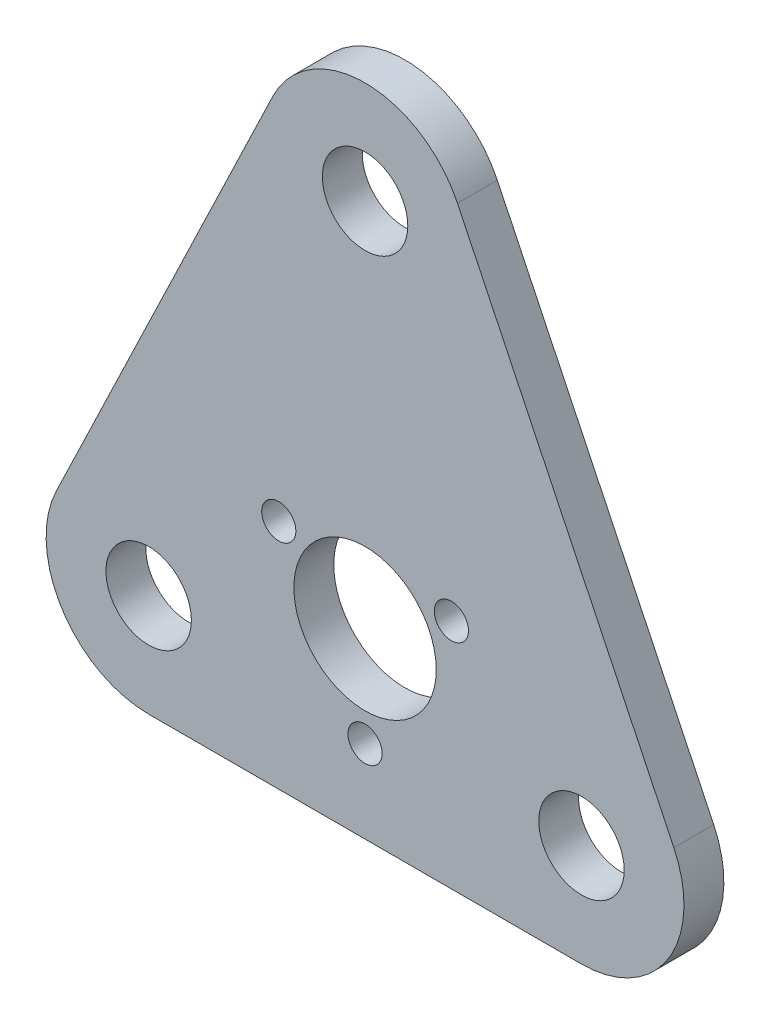
SolidWorks part; units mm, degrees
ref_plane "Front Plane" through (0, 0, 0) normal (0, 0, 1) x (1, 0, 0)
ref_plane "Top Plane" through (0, 0, 0) normal (0, 1, 0) x (1, 0, 0)
ref_plane "Right Plane" through (0, 0, 0) normal (1, 0, 0) x (0, 0, -1)
sketch "Sketch1" plane through (0, 0, 0) normal (0, 0, 1) x (1, 0, 0)
  line L0 (-38, 0) -> (38, 0) construction
  line L1 (-38, -18) -> (38, -18)
  line L2 (0, -18) -> (0, 14) construction
  line L3 (-32.3193, 14) -> (32.3193, 14) construction
  line L4 (0, 14) -> (-24.6565, 28.2354) construction
  line L5 (0, 14) -> (0, 79) construction
  line L6 (16.221, 86.8025) -> (54.221, 7.8025)
  line L7 (-16.221, 86.8025) -> (-54.221, 7.8025)
  circle A0 centre (-38, 0) radius 7.5
  circle A1 centre (38, 0) radius 7.5
  arc A2 (-54.221, 7.8025) -> (-38, -18) centre (-38, 0) ccw
  arc A3 (38, -18) -> (54.221, 7.8025) centre (38, 0) ccw
  circle A4 centre (0, 14) radius 12.5
  circle A6 centre (-15.1554, 22.75) radius 3
  circle A7 centre (0, -3.5) radius 3
  circle A8 centre (15.1554, 22.75) radius 3
  circle A9 centre (0, 79) radius 7.5
  arc A10 (16.221, 86.8025) -> (-16.221, 86.8025) centre (0, 79) ccw
  point P4 (0, 0)
  point P18 (0, 14)
  point P30 (-3.1358, 101.4343)
  dimension "D1" = 30
  dimension "D2" = 36
  dimension "D3" = 15
  dimension "D5" = 25
  dimension "D6" = 6
  dimension "D7" = 6
  dimension "D8" = 6
  dimension "D9" = 36
  dimension "D10" = 15
  dimension "D15" = 15
  dimension "D4" = 97
  dimension "D11" = 76
  dimension "D12" = 32
  dimension "D13" = 14.5
  dimension "D14" = 40.75
  dimension "D16" = 40.75
  dimension "D17" = 30.3109
extrude "Boss-Extrude1" add sketch "Sketch1" along normal mid plane 7
